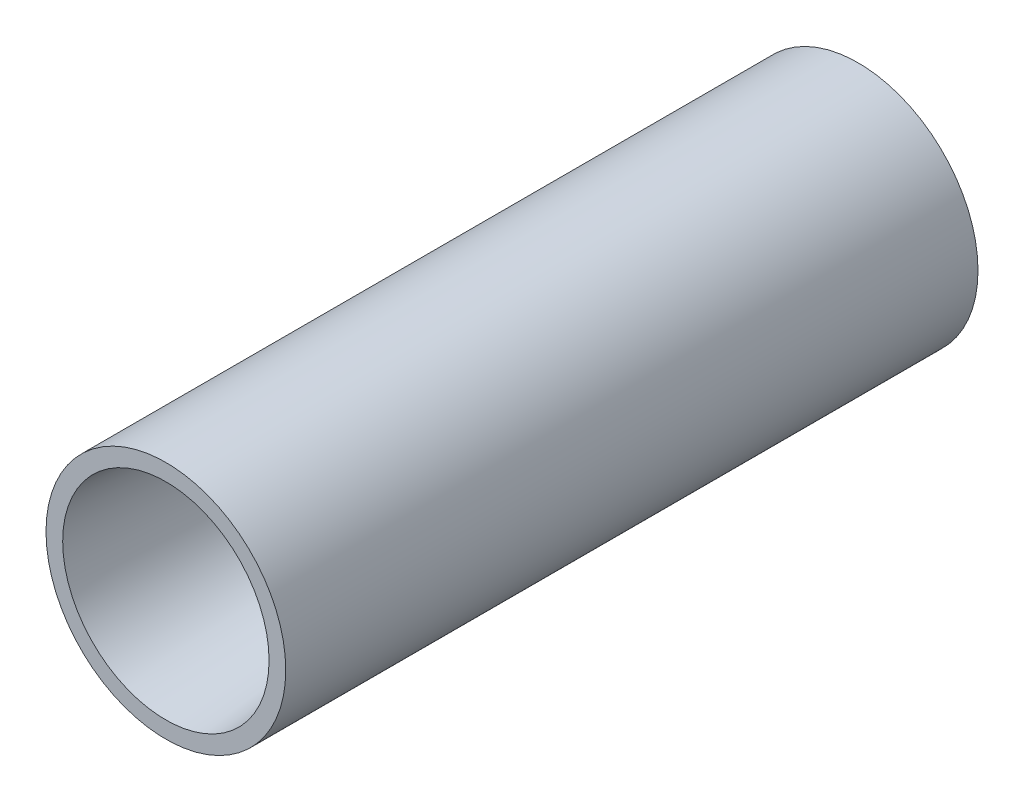
SolidWorks part; units mm, degrees
ref_plane "Front Plane" through (0, 0, 0) normal (0, 0, 1) x (1, 0, 0)
ref_plane "Top Plane" through (0, 0, 0) normal (0, 1, 0) x (1, 0, 0)
ref_plane "Right Plane" through (0, 0, 0) normal (1, 0, 0) x (0, 0, -1)
sketch "Sketch1" plane through (0, 0, 0) normal (0, 0, 1) x (1, 0, 0)
  circle A0 centre (0, 0) radius 12.1219
extrude "Boss-Extrude1" add sketch "Sketch1" along normal blind 70
sketch "Sketch2" plane through (0, 0, 70) normal (0, 0, 1) x (1, 0, 0)
  circle A0 centre (0, 0) radius 6.4354
extrude "Cut-Extrude1" cut sketch "Sketch2" against normal blind 60
chamfer "Chamfer1" distance 4 angle 85 1 edges at (6.4354, 0, 70)
